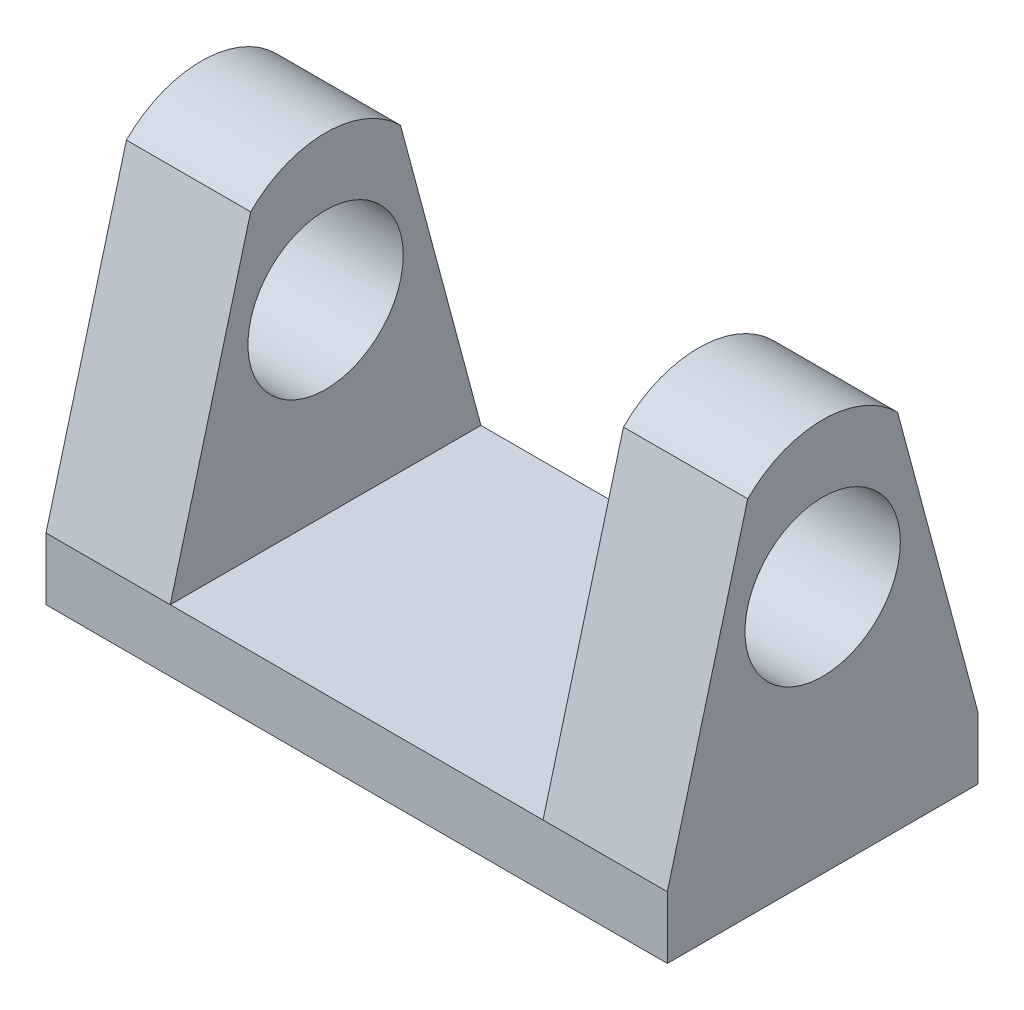
SolidWorks part; units mm, degrees
material "ABS"
ref_plane "Front Plane" through (0, 0, 0) normal (0, 0, 1) x (1, 0, 0)
ref_plane "Top Plane" through (0, 0, 0) normal (0, 1, 0) x (1, 0, 0)
ref_plane "Right Plane" through (0, 0, 0) normal (1, 0, 0) x (0, 0, -1)
sketch "Sketch1" plane through (0, 0, 0) normal (0, 1, 0) x (1, 0, 0)
  line L1 (-12.7, -6.35) -> (12.7, -6.35)
  line L2 (-12.7, -6.35) -> (-12.7, 6.35)
  line L3 (-12.7, 6.35) -> (12.7, 6.35)
  line L4 (12.7, -6.35) -> (12.7, 6.35)
  line L5 (-12.7, -6.35) -> (12.7, 6.35) construction
  line L6 (-12.7, 6.35) -> (12.7, -6.35) construction
  point P0 (0, 0)
  dimension "D1" = 25.4
  dimension "D2" = 12.7
extrude "Boss-Extrude1" add sketch "Sketch1" along normal blind 2.54
sketch "Sketch2" plane through (12.7, 0, 0) normal (1, 0, 0) x (0, 0, -1)
  line L0 (-6.35, 2.54) -> (-3.063, 14.8073)
  line L1 (6.35, 2.54) -> (3.063, 14.8073)
  line L2 (-6.35, 2.54) -> (6.35, 2.54) construction
  line L3 (-6.35, 2.54) -> (6.35, 2.54)
  arc A1 (-3.063, 14.8073) -> (3.063, 14.8073) centre (0, 11.7443) cw
  dimension "D1" = 75
  dimension "D2" = 75
extrude "Boss-Extrude2" add sketch "Sketch2" against normal blind 5.08
ref_plane "Plane1" through (0, 0, 0) normal (1, 0, 0) x (0, 0, -1)
mirror "Mirror1" about plane through (0, 0, 0) normal (1, 0, 0) of "Boss-Extrude2"
sketch "Sketch3" plane through (12.7, 0, 0) normal (1, 0, 0) x (0, 0, -1)
  line L0 (-6.35, 0) -> (6.35, 0) construction
  circle A0 centre (0, 10.16) radius 3.175
  dimension "D1" = 10.16
extrude "Cut-Extrude1" cut sketch "Sketch3" against normal through all
